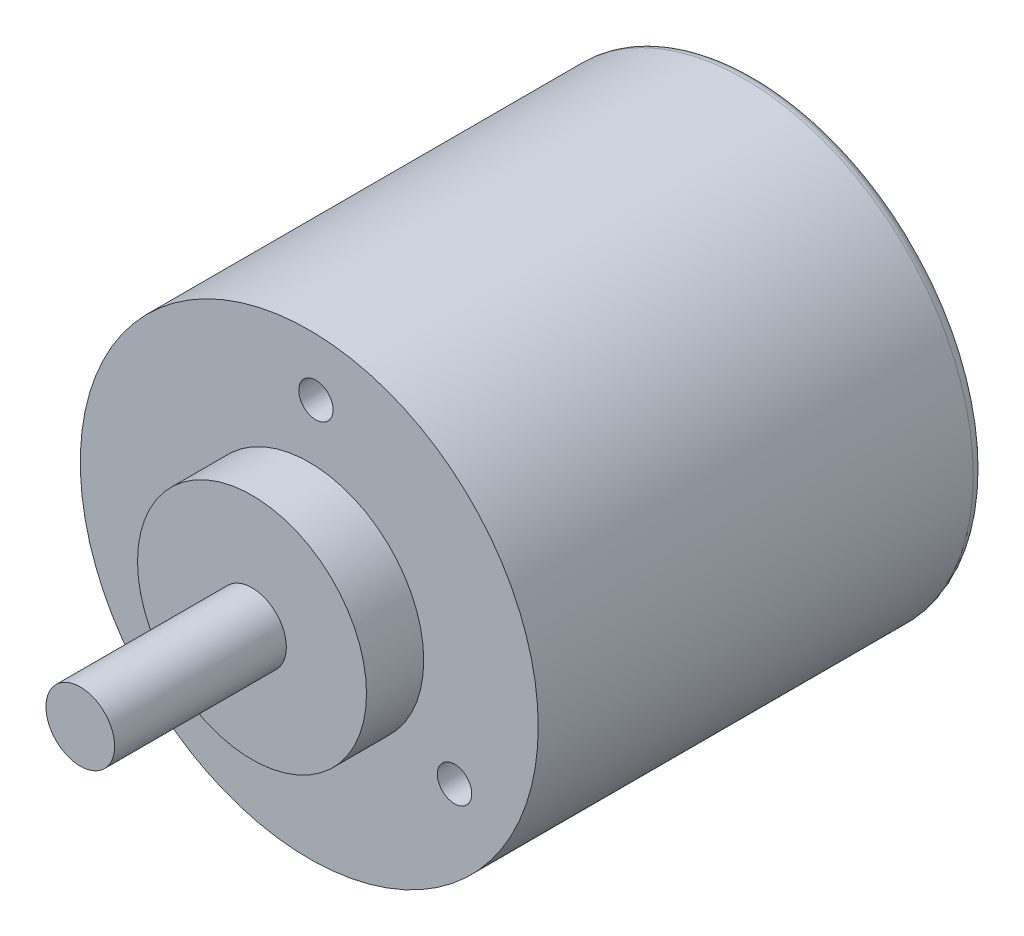
SolidWorks part; units mm, degrees
ref_plane "Front Plane" through (0, 0, 0) normal (0, 0, 1) x (1, 0, 0)
ref_plane "Top Plane" through (0, 0, 0) normal (0, 1, 0) x (1, 0, 0)
ref_plane "Right Plane" through (0, 0, 0) normal (1, 0, 0) x (0, 0, -1)
sketch "Sketch1" plane through (0, 0, 0) normal (0, 0, 1) x (1, 0, 0)
  circle A0 centre (0, 0) radius 20
extrude "Boss-Extrude1" add sketch "Sketch1" along normal blind 39
sketch "Sketch2" plane through (0, 0, 39) normal (0, 0, 1) x (1, 0, 0)
  circle A0 centre (0, 0) radius 10
extrude "Boss-Extrude2" add sketch "Sketch2" along normal blind 5
sketch "Sketch3" plane through (0, 0, 44) normal (0, 0, 1) x (1, 0, 0)
  circle A0 centre (0, 0) radius 3
extrude "Boss-Extrude3" add sketch "Sketch3" along normal blind 15
fillet "Fillet1" radius 1 1 edges at (20, 0, 0)
sketch "Sketch4" plane through (0, 0, 39) normal (0, 0, 1) x (1, 0, 0)
  circle A0 centre (0.5807, 14.9888) radius 1.5
  circle A1 centre (0, 0) radius 20 construction
  dimension "D2" = 3
  dimension "D1" = 15
extrude "Cut-Extrude1" cut sketch "Sketch4" against normal blind 5
pattern_circular "CirPattern1" count 3 over 360 about axis through (0, 0, 0) along (0, 0, 1) of "Cut-Extrude1"
